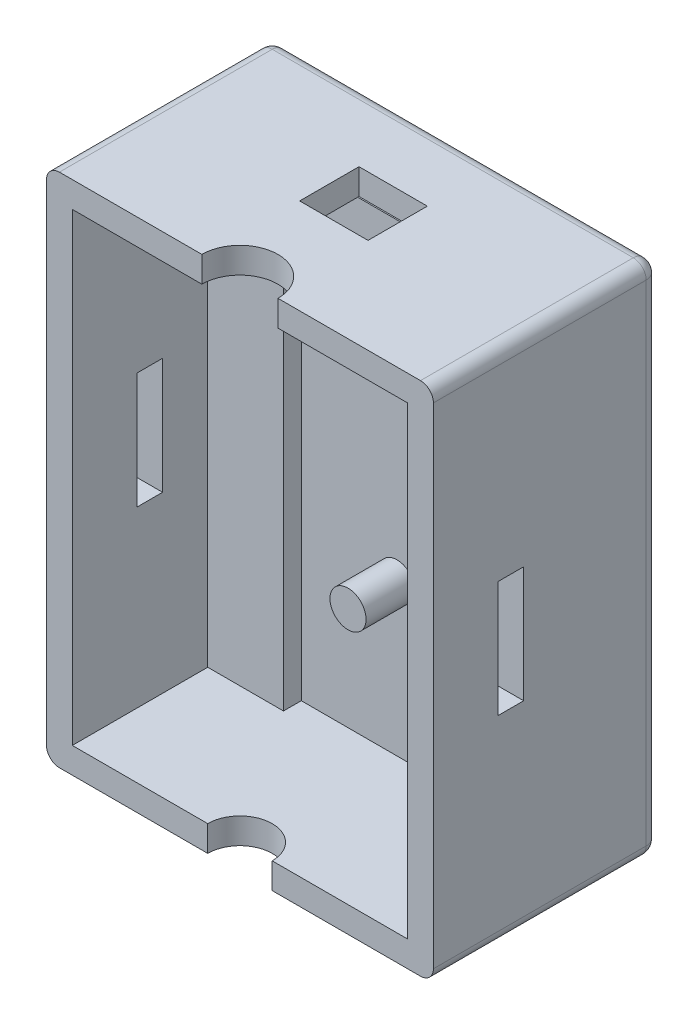
SolidWorks part; units mm, degrees
ref_plane "Front Plane" through (0, 0, 0) normal (0, 0, 1) x (1, 0, 0)
ref_plane "Top Plane" through (0, 0, 0) normal (0, 1, 0) x (1, 0, 0)
ref_plane "Right Plane" through (0, 0, 0) normal (1, 0, 0) x (0, 0, -1)
sketch "Sketch1" plane through (0, 0, 0) normal (0, 0, 1) x (1, 0, 0)
  line L1 (-15, 20) -> (15, 20)
  line L2 (-15, 20) -> (-15, -20)
  line L3 (-15, -20) -> (15, -20)
  line L4 (15, 20) -> (15, -20)
  line L5 (-15, 20) -> (15, -20) construction
  line L6 (-15, -20) -> (15, 20) construction
  point P0 (0, 0)
  dimension "D1" = 30
  dimension "D2" = 40
extrude "Boss-Extrude1" add sketch "Sketch1" along normal blind 17.5
sketch "Sketch2" plane through (0, 0, 17.5) normal (0, 0, 1) x (1, 0, 0)
  line L0 (15, 20) -> (-15, 20) construction
  line L1 (-13, 18) -> (13, 18)
  line L4 (13, 18) -> (13, -18)
  line L6 (-13, -18) -> (-13, 18)
  line L7 (15, -20) -> (15, 20) construction
  line L11 (13, -18) -> (-13, -18)
  point P0 (0, 0)
  dimension "D1" = 2
  dimension "D2" = 2
extrude "Cut-Extrude1" cut sketch "Sketch2" against normal blind 15.5
sketch "Sketch6" plane through (0, 0, 2) normal (0, 0, 1) x (1, 0, 0)
  line L0 (0, 18) -> (-7.125, 18)
  line L1 (13, 18) -> (-13, 18) construction
  line L2 (0, 18) -> (7.125, 18)
  line L3 (13, 18) -> (-13, 18) construction
  line L4 (-7.125, 18) -> (-7.125, -13)
  line L6 (7.125, -13) -> (7.125, 18)
  line L7 (7.125, -13) -> (7.125, -18)
  line L8 (-13, -18) -> (13, -18) construction
  line L9 (-7.125, -13) -> (-7.125, -18)
  line L10 (-13, -18) -> (13, -18) construction
  line L11 (-7.125, -18) -> (7.125, -18)
  dimension "D1" = 7.125
  dimension "D2" = 7.125
  dimension "D3" = 31
extrude "Boss-Extrude2" add sketch "Sketch6" along normal blind 3.62
sketch "Sketch10" plane through (13, 0, 0) normal (-1, 0, 0) x (0, 0, 1)
  line L4 (12.5, 0) -> (12.5, -4.5)
  line L5 (12.5, -4.5) -> (10.5, -4.5)
  line L6 (10.5, 0) -> (10.5, -4.5)
  line L8 (12.5, 0) -> (12.5, 4.5)
  line L9 (12.5, 4.5) -> (10.5, 4.5)
  line L10 (10.5, 0) -> (10.5, 4.5)
  dimension "D2" = 2
  dimension "D3" = 4.5
  dimension "D4" = 4.5
extrude "Cut-Extrude5" cut sketch "Sketch10" against normal through all both and the other way through all
sketch "Sketch12" plane through (0, -18, 0) normal (0, 1, 0) x (1, 0, 0)
  line L0 (-13, -17.5) -> (13, -17.5) construction
  line L1 (2.5, -17.5) -> (-2.5, -17.5)
  arc A0 (2.5, -17.5) -> (-2.5, -17.5) centre (0, -17.5) ccw
  dimension "D1" = 5
extrude "Cut-Extrude6" cut sketch "Sketch12" against normal through all
sketch "Sketch13" plane through (0, 0, 2) normal (0, 0, 1) x (1, 0, 0)
  line L1 (-13, 18) -> (-7.125, 18)
  line L2 (-13, 18) -> (-13, -18)
  line L3 (-13, -18) -> (-7.125, -18)
  line L4 (-7.125, 18) -> (-7.125, -18)
  line L5 (7.125, 18) -> (13, 18)
  line L6 (7.125, 18) -> (7.125, -18)
  line L7 (7.125, -18) -> (13, -18)
  line L8 (13, 18) -> (13, -18)
extrude "Boss-Extrude4" add sketch "Sketch13" along normal blind 5
sketch "Sketch14" plane through (0, 20, 0) normal (0, 1, 0) x (1, 0, 0)
  line L0 (15, -17.5) -> (-15, -17.5) construction
  line L1 (2.95, -17.5) -> (-2.95, -17.5)
  arc A0 (2.95, -17.5) -> (-2.95, -17.5) centre (0, -17.5) ccw
  dimension "D1" = 5.9
extrude "Cut-Extrude7" cut sketch "Sketch14" against normal up to next
sketch "Sketch15" plane through (0, 18, 0) normal (0, -1, 0) x (1, 0, 0)
  line L0 (-2.75, 10.12) -> (-2.75, 5.52)
  line L5 (2.55, 5.52) -> (2.55, 7.82)
  line L10 (2.55, 7.82) -> (2.55, 10.12)
  line L11 (-2.75, 10.12) -> (2.55, 10.12)
  line L12 (-2.75, 5.52) -> (2.55, 5.52)
  point P3 (-2.75, 7.82)
  dimension "D1" = 2.3
  dimension "D2" = 2.3
  dimension "D3" = 5.3
  dimension "D4" = 4.6
extrude "Cut-Extrude8" cut sketch "Sketch15" against normal through all
sketch "Sketch16" plane through (0, 0, 5.62) normal (0, 0, 1) x (1, 0, 0)
  circle A0 centre (0.3, -6.225) radius 1.4
  dimension "D1" = 2.8
extrude "Boss-Extrude5" add sketch "Sketch16" along normal blind 3.8
fillet "Fillet1" radius 1 8 edges at (-15, 20, 8.75) (15, 20, 8.75) (15, -20, 8.75) (-15, -20, 8.75) (0, -20, 0) (-15, 0, 0) (15, 0, 0) (0, 20, 0)
